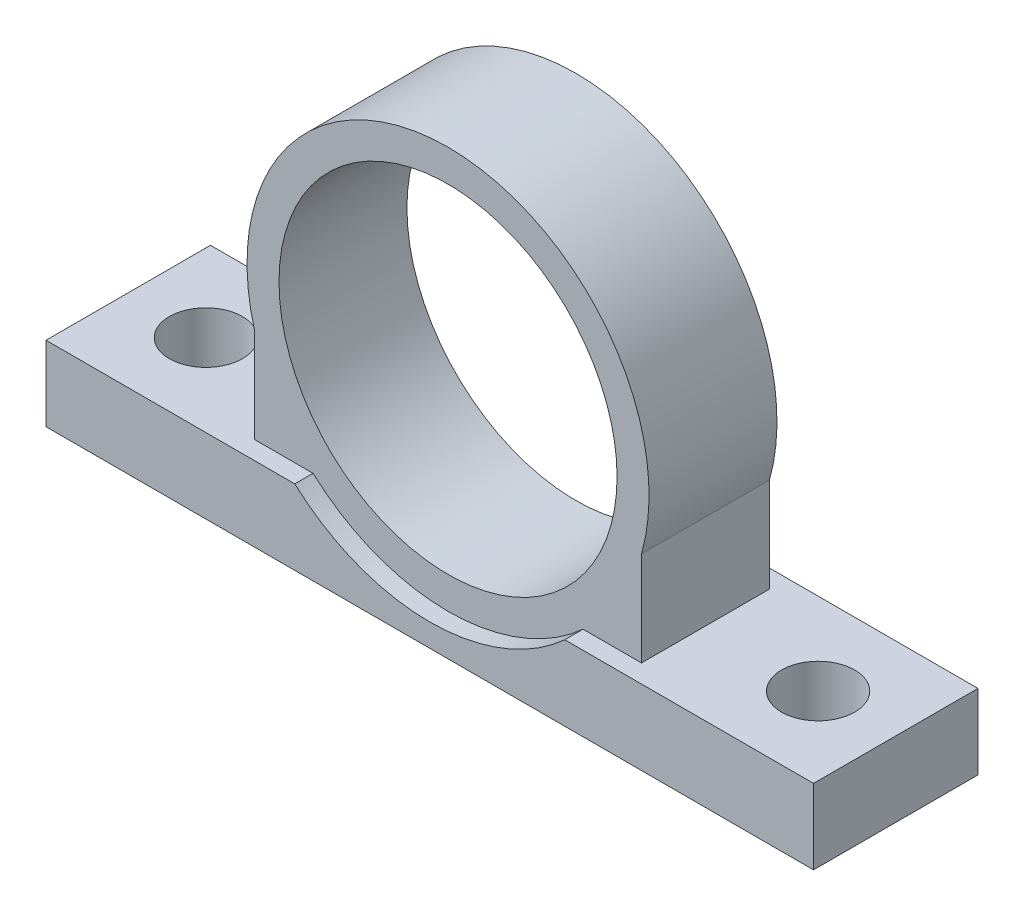
SolidWorks part; units mm, degrees
ref_plane "Alzado" through (0, 0, 0) normal (0, 0, 1) x (1, 0, 0)
ref_plane "Planta" through (0, 0, 0) normal (0, 1, 0) x (1, 0, 0)
ref_plane "Vista lateral" through (0, 0, 0) normal (1, 0, 0) x (0, 0, -1)
sketch "Croquis1" plane through (0, 0, 0) normal (0, 0, 1) x (1, 0, 0)
  line L0 (0, 0) -> (-84, 0)
  line L1 (-84, 0) -> (-84, 8.2)
  line L2 (-84, 8.2) -> (-63.1753, 8.2)
  line L3 (0, 8.2) -> (0, 0)
  line L4 (-42, 0) -> (-42, 24.5) construction
  line L7 (-63.1753, 8.2) -> (-63.1753, 18.5329)
  line L8 (-20.8247, 8.2) -> (-20.8247, 18.5329)
  line L10 (-20.8247, 8.2) -> (0, 8.2)
  arc A0 (-20.8247, 18.5329) -> (-63.1753, 18.5329) centre (-42, 24.5) ccw
  circle A1 centre (-42, 24.5) radius 18.5
  dimension "D4" = 44
  dimension "D7" = 37
  dimension "D1" = 84
  dimension "D2" = 8.2
  dimension "D3" = 24.5
extrude "Saliente-Extruir1" add sketch "Croquis1" along normal blind 18
sketch "Croquis2" plane through (0, 0, 18) normal (0, 0, 1) x (1, 0, 0)
  line L0 (-20.8247, 8.2) -> (-27.2247, 8.2)
  line L1 (-63.1753, 8.2) -> (-63.1753, 18.5329)
  line L2 (-20.8247, 8.2) -> (-20.8247, 18.5329)
  line L3 (-56.7753, 8.2) -> (-63.1753, 8.2)
  circle A1 centre (-42, 24.5) radius 17.5
  arc A2 (-20.8247, 18.5329) -> (-63.1753, 18.5329) centre (-42, 24.5) ccw
  arc A3 (-56.7753, 8.2) -> (-27.2247, 8.2) centre (-42, 24.5) ccw
extrude "Cortar-Extruir1" cut sketch "Croquis2" against normal blind 2
ref_plane "Plano1" through (0, 0, 9) normal (0, 0, 1) x (1, 0, 0)
mirror "Simetría1" about plane through (0, 0, 9) normal (0, 0, 1) of "Cortar-Extruir1"
sketch "Croquis3" plane through (0, 8.2, 0) normal (0, 1, 0) x (1, 0, 0)
  line L0 (0, -9) -> (-8.5, -9) construction
  line L1 (0, -18) -> (0, 0) construction
  line L2 (-8.5, -9) -> (-8.5, 0) construction
  line L3 (0, 0) -> (-27.2247, 0) construction
  circle A0 centre (-8.5, -9) radius 4
  dimension "D1" = 8.5
extrude "Cortar-Extruir2" cut sketch "Croquis3" against normal through all
ref_plane "Plano2" through (-42, 0, 0) normal (1, 0, 0) x (0, 0, -1)
mirror "Simetría2" about plane through (-42, 0, 0) normal (1, 0, 0) of "Cortar-Extruir2"
